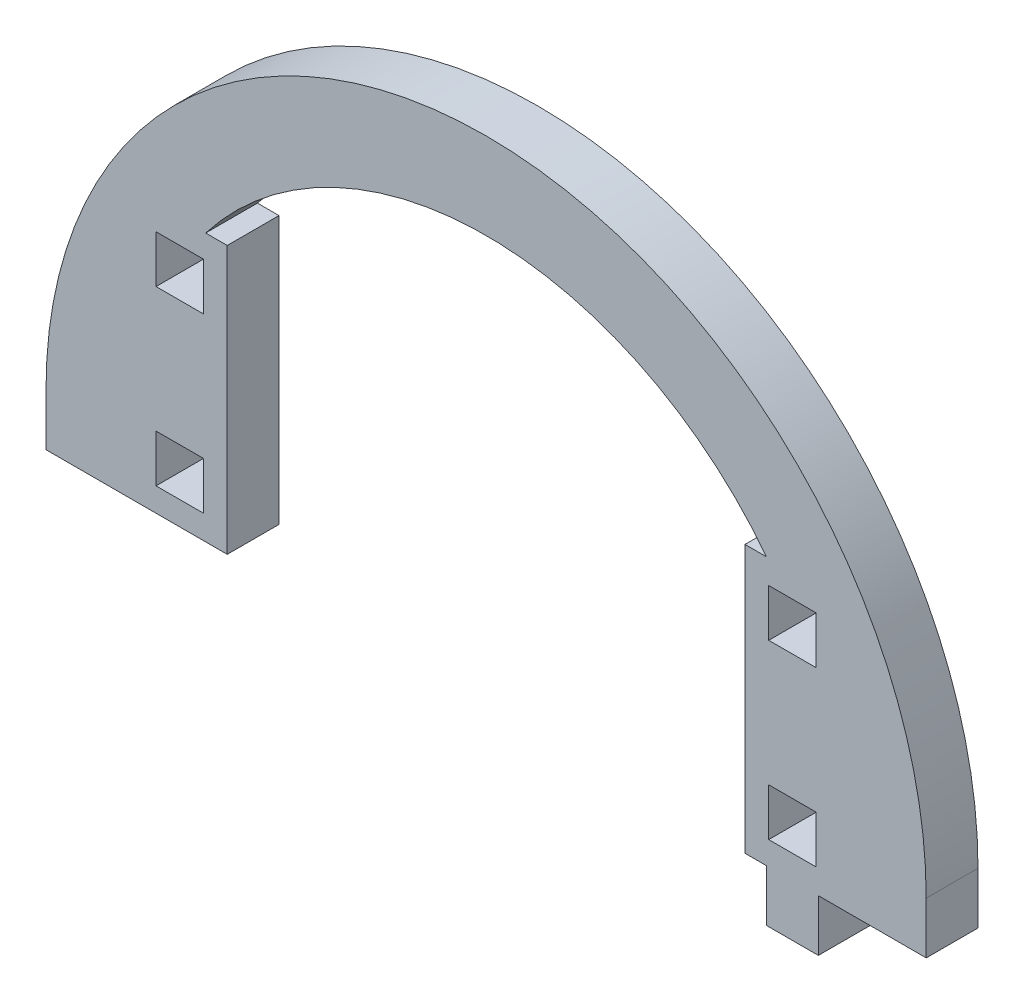
SolidWorks part; units mm, degrees
ref_plane "Front Plane" through (0, 0, 0) normal (0, 0, 1) x (1, 0, 0)
ref_plane "Top Plane" through (0, 0, 0) normal (0, 1, 0) x (1, 0, 0)
ref_plane "Right Plane" through (0, 0, 0) normal (1, 0, 0) x (0, 0, -1)
sketch "Model" plane through (0, 0, 0) normal (0, 0, 1) x (1, 0, 0)
  line L0 (3357.0323, 1716.9944) -> (3357.0323, 1710.9944)
  line L1 (3459.0323, 1716.9944) -> (3459.0323, 1710.9944)
  line L2 (3367.0323, 1710.9944) -> (3357.0323, 1710.9944)
  line L3 (3446.2823, 1719.2444) -> (3440.7823, 1719.2444)
  line L4 (3440.7823, 1719.2444) -> (3440.7823, 1713.7444)
  line L5 (3440.7823, 1713.7444) -> (3446.2823, 1713.7444)
  line L6 (3446.2823, 1713.7444) -> (3446.2823, 1719.2444)
  line L7 (3438.0323, 1710.9944) -> (3440.5323, 1710.9944)
  line L8 (3440.5323, 1710.9944) -> (3440.5323, 1704.9944)
  line L9 (3440.5323, 1704.9944) -> (3446.5323, 1704.9944)
  line L10 (3446.5323, 1704.9944) -> (3446.5323, 1710.9944)
  line L11 (3446.2823, 1739.2444) -> (3440.7823, 1739.2444)
  line L12 (3440.7823, 1739.2444) -> (3440.7823, 1733.7444)
  line L13 (3440.7823, 1733.7444) -> (3446.2823, 1733.7444)
  line L14 (3446.2823, 1733.7444) -> (3446.2823, 1739.2444)
  line L15 (3440.5284, 1741.9944) -> (3438.0323, 1741.9944)
  line L16 (3375.2823, 1719.2444) -> (3369.7823, 1719.2444)
  line L17 (3369.7823, 1719.2444) -> (3369.7823, 1713.7444)
  line L18 (3369.7823, 1713.7444) -> (3375.2823, 1713.7444)
  line L19 (3375.2823, 1713.7444) -> (3375.2823, 1719.2444)
  line L20 (3367.0323, 1710.9944) -> (3378.0323, 1710.9944)
  line L21 (3375.2823, 1739.2444) -> (3369.7823, 1739.2444)
  line L22 (3369.7823, 1739.2444) -> (3369.7823, 1733.7444)
  line L23 (3369.7823, 1733.7444) -> (3375.2823, 1733.7444)
  line L24 (3375.2823, 1733.7444) -> (3375.2823, 1739.2444)
  line L25 (3378.0323, 1741.9944) -> (3375.5361, 1741.9944)
  line L26 (3378.0323, 1741.9944) -> (3378.0323, 1710.9944)
  line L27 (3438.0323, 1741.9944) -> (3438.0323, 1710.9944)
  line L28 (3446.5323, 1710.9944) -> (3459.0323, 1710.9944)
  arc A0 (3459.0323, 1716.9944) -> (3357.0323, 1716.9944) centre (3408.0323, 1716.9944) ccw
  arc A1 (3440.5284, 1741.9944) -> (3375.5361, 1741.9944) centre (3408.0323, 1716.9944) ccw
extrude "Boss-Extrude1" add sketch "Model" along normal blind 6 contours L18 L19 L16 L17 | L13 L14 L11 L12 | L5 L6 L3 L4 | A0 L0 L2 L20 L26 L25 A1 L15 L27 L7 L8 L9 L10 L28 L1 | L22 L23 L24 L21
